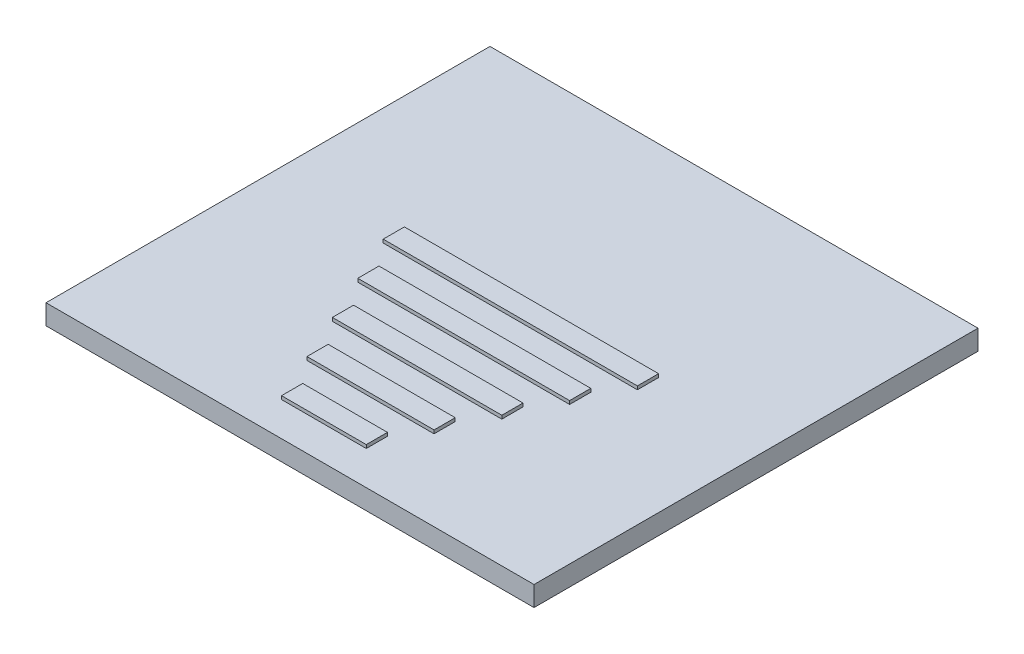
SolidWorks part; units mm, degrees
ref_plane "Front Plane" through (0, 0, 0) normal (0, 0, 1) x (1, 0, 0)
ref_plane "Top Plane" through (0, 0, 0) normal (0, 1, 0) x (1, 0, 0)
ref_plane "Right Plane" through (0, 0, 0) normal (1, 0, 0) x (0, 0, -1)
sketch "Sketch1" plane through (0, 0, 0) normal (0, 1, 0) x (1, 0, 0)
  line L5 (18.288, -16.637) -> (-18.288, -16.637)
  line L6 (18.288, -16.637) -> (18.288, 16.637)
  line L11 (18.288, 16.637) -> (-18.288, 16.637)
  line L12 (-18.288, -16.637) -> (-18.288, 16.637)
  line L13 (18.288, -16.637) -> (-18.288, 16.637) construction
  line L14 (18.288, 16.637) -> (-18.288, -16.637) construction
  point P0 (0, 0)
  dimension "D1" = 33.274
  dimension "D2" = 36.576
extrude "Boss-Extrude1" add sketch "Sketch1" along normal blind 1.5
sketch "Sketch2" plane through (0, 1.5, 0) normal (0, 1, 0) x (1, 0, 0)
  line L0 (0, -0.127) -> (0, -14.097) construction
  line L1 (-9.525, 1.4605) -> (9.525, 1.4605)
  line L2 (-9.525, 1.4605) -> (-9.525, -0.127)
  line L3 (-9.525, -0.127) -> (9.525, -0.127)
  line L4 (9.525, 1.4605) -> (9.525, -0.127)
  line L5 (-6.35, -5.5245) -> (6.35, -5.5245)
  line L6 (-6.35, -5.5245) -> (-6.35, -7.112)
  line L7 (-6.35, -7.112) -> (6.35, -7.112)
  line L8 (6.35, -5.5245) -> (6.35, -7.112)
  line L9 (-4.7625, -9.017) -> (4.7625, -9.017)
  line L10 (-4.7625, -9.017) -> (-4.7625, -10.6045)
  line L11 (-4.7625, -10.6045) -> (4.7625, -10.6045)
  line L12 (4.7625, -9.017) -> (4.7625, -10.6045)
  line L13 (-3.175, -12.5095) -> (3.175, -12.5095)
  line L14 (-3.175, -12.5095) -> (-3.175, -14.097)
  line L15 (-3.175, -14.097) -> (3.175, -14.097)
  line L16 (3.175, -12.5095) -> (3.175, -14.097)
  line L17 (-6.35, -0.127) -> (-6.35, -2.032) construction
  line L18 (-7.9375, -2.032) -> (7.9375, -2.032)
  line L19 (-7.9375, -2.032) -> (-7.9375, -3.6195)
  line L20 (-7.9375, -3.6195) -> (7.9375, -3.6195)
  line L21 (7.9375, -2.032) -> (7.9375, -3.6195)
  line L22 (-5.8622, -3.6195) -> (-5.8622, -5.5245) construction
  line L23 (-4.0842, -7.112) -> (-4.0842, -9.017) construction
  line L24 (-2.3062, -12.5095) -> (-2.3062, -10.6045) construction
  line L26 (-18.288, -16.637) -> (18.288, -16.637) construction
  point P18 (0, -14.097)
  point P19 (0, -12.5095)
  point P20 (0, -10.6045)
  point P21 (0, -7.112)
  point P22 (0, -3.6195)
  dimension "D1" = 19.05
  dimension "D2" = 12.7
  dimension "D3" = 9.525
  dimension "D4" = 6.35
  dimension "D5" = 1.5875
  dimension "D6" = 15.875
  dimension "D7" = 1.905
  dimension "D8" = 2.54
extrude "Boss-Extrude2" add sketch "Sketch2" along normal blind 0.254
